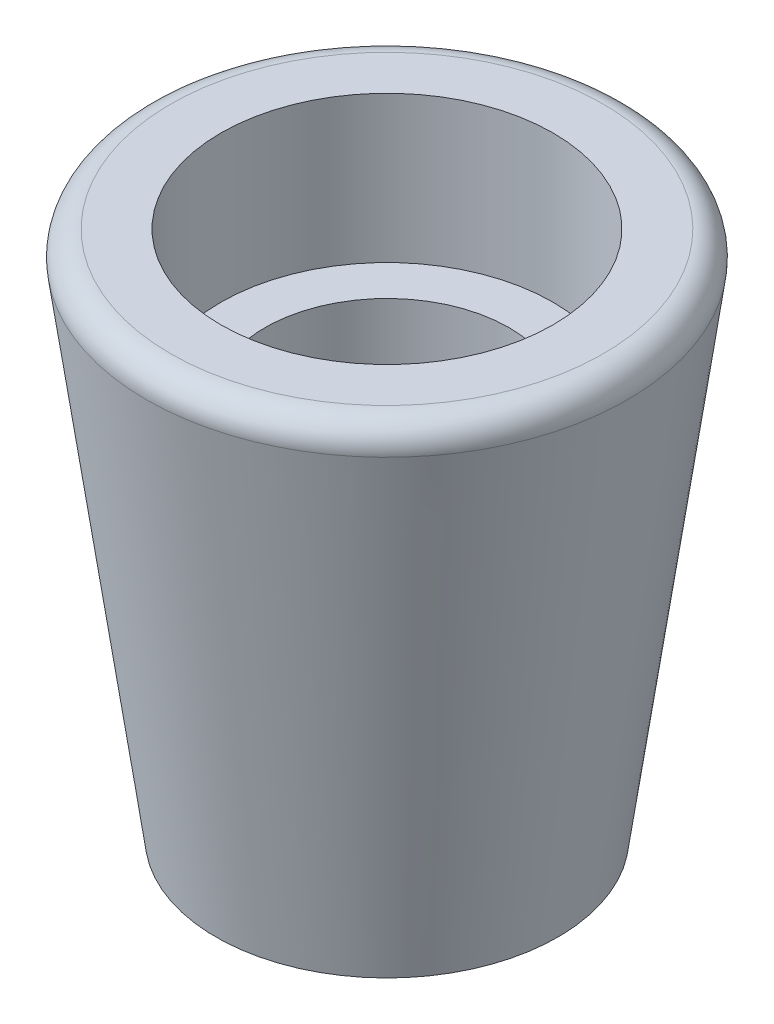
SolidWorks part; units mm, degrees
ref_plane "Front Plane" through (0, 0, 0) normal (0, 0, 1) x (1, 0, 0)
ref_plane "Top Plane" through (0, 0, 0) normal (0, 1, 0) x (1, 0, 0)
ref_plane "Right Plane" through (0, 0, 0) normal (1, 0, 0) x (0, 0, -1)
sketch "Sketch1" plane through (0, 0, 0) normal (0, 0, 1) x (1, 0, 0)
  line L0 (0, 0) -> (0, 12.39) construction
  line L1 (2.5, 0) -> (3.5, 0)
  line L2 (3.5, 0) -> (5, 10.8)
  line L3 (5, 10.8) -> (3.4, 10.8)
  line L4 (3.4, 10.8) -> (3.4, 7.8)
  line L5 (3.4, 7.8) -> (2.5, 7.8)
  line L7 (2.5, 7.8) -> (2.5, 0)
  line L8 (2.5, 0) -> (0, 0) construction
  dimension "D1" = 2.5
  dimension "D2" = 3.5
  dimension "D3" = 10.8
  dimension "D4" = 5
  dimension "D5" = 3
  dimension "D6" = 3.4
revolve "Revolve1" add sketch "Sketch1" angle 360 about L0
fillet "Fillet1" radius 0.5 1 edges at (0, 10.8, -5)
